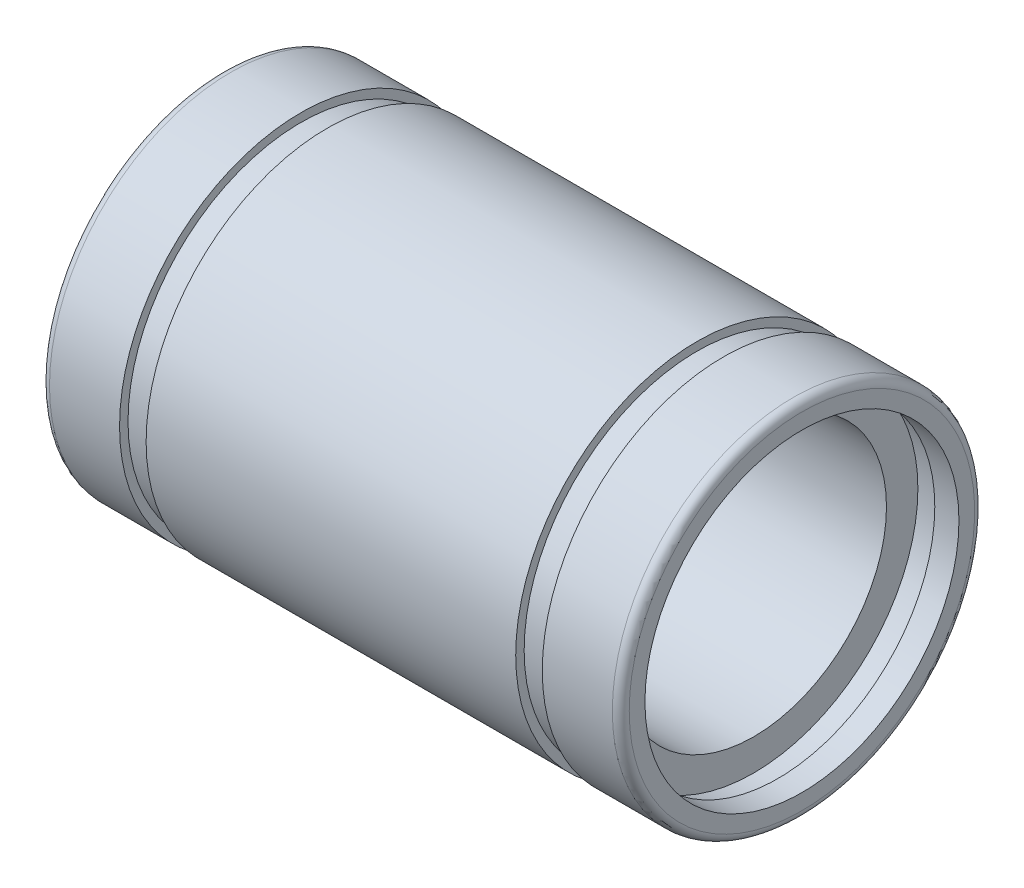
SolidWorks part; units mm, degrees
ref_plane "Front" through (0, 0, 0) normal (0, 0, 1) x (1, 0, 0)
ref_plane "Top" through (0, 0, 0) normal (0, 1, 0) x (1, 0, 0)
ref_plane "Right" through (0, 0, 0) normal (1, 0, 0) x (0, 0, -1)
sketch "Sketch2" plane through (0, 0, 0) normal (0, 0, 1) x (1, 0, 0)
  line L0 (12, 5.5) -> (12, 7.5) construction
  line L1 (24, 7.15) -> (24, 6.5)
  line L2 (20.75, 7.15) -> (19.65, 7.15)
  line L3 (20.75, 7.5) -> (20.75, 7.15)
  line L4 (19.65, 7.15) -> (19.65, 7.5)
  line L5 (19.65, 7.5) -> (4.35, 7.5)
  line L6 (20.75, 7.5) -> (23.65, 7.5)
  line L7 (4.35, 7.5) -> (4.35, 7.15)
  line L8 (4.35, 7.15) -> (3.25, 7.15)
  line L9 (3.25, 7.15) -> (3.25, 7.5)
  line L10 (3.25, 7.5) -> (0.35, 7.5)
  line L11 (0, 7.15) -> (0, 6.5)
  line L12 (2, 5.5) -> (22, 5.5)
  line L13 (22, 5.5) -> (22, 6.8)
  line L14 (22, 6.8) -> (23, 6.8)
  line L15 (23, 6.8) -> (23, 6.5)
  line L16 (23, 6.5) -> (24, 6.5)
  line L17 (2, 6.8) -> (2, 5.5)
  line L18 (2, 6.8) -> (1, 6.8)
  line L19 (1, 6.8) -> (1, 6.5)
  line L20 (1, 6.5) -> (0, 6.5)
  line L21 (0, 0) -> (26.8504, 0) construction
  arc A0 (24, 7.15) -> (23.65, 7.5) centre (23.65, 7.15) ccw
  arc A1 (0, 7.15) -> (0.35, 7.5) centre (0.35, 7.15) cw
  point P18 (0, 7.5)
  dimension "D11" = 0.65
  dimension "D12" = 1.1
  dimension "D6" = 0.35
  dimension "D1" = 5.5
  dimension "D2" = 2
  dimension "D3" = 20
  dimension "D4" = 24
  dimension "D5" = 15.3
  dimension "D7" = 1
  dimension "D8" = 1.3
  dimension "D9" = 1
  dimension "D10" = 0.3
  dimension "D13" = 0.35
revolve "Revolve1" add sketch "Sketch2" angle 360 about L21
equation "\"rod_length_xaxis\"= 300.7"
equation "\"linear-xbar-dia\"= 8mm ' Diameter of the metal slide bar used on the X Axis"
